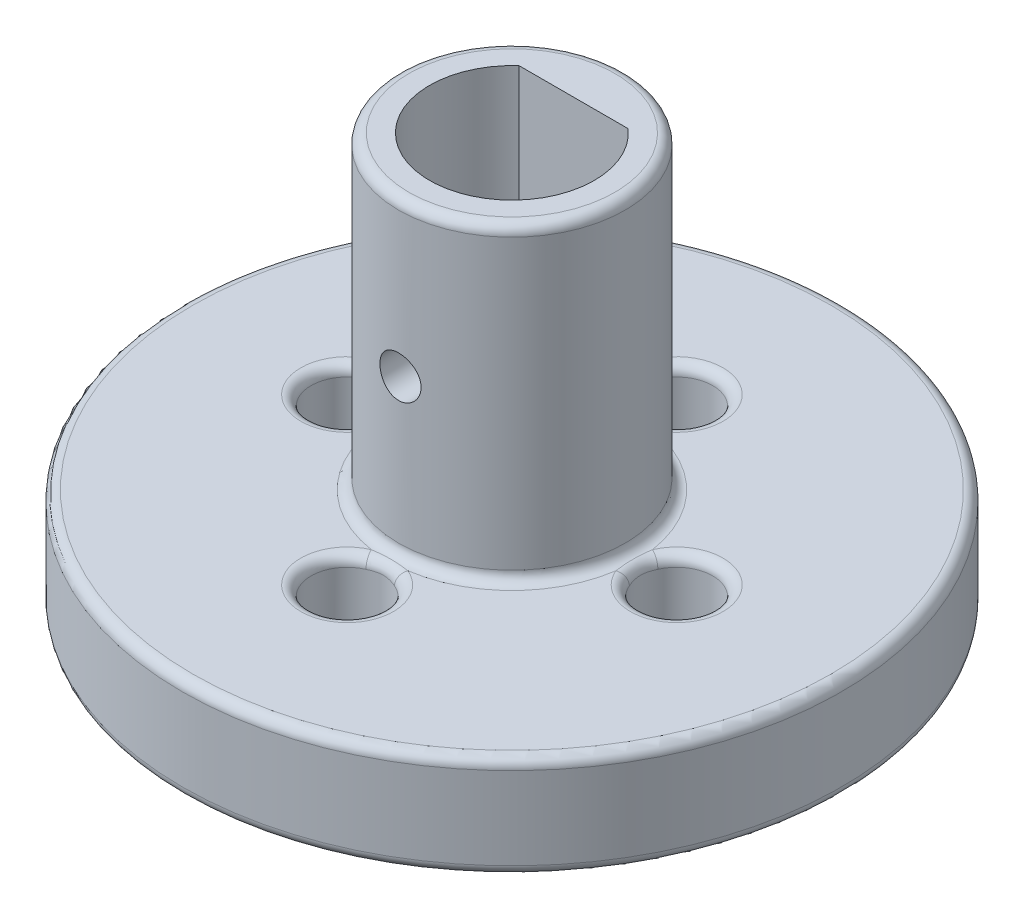
SolidWorks part; units mm, degrees
ref_plane "Front Plane" through (0, 0, 0) normal (0, 0, 1) x (1, 0, 0)
ref_plane "Top Plane" through (0, 0, 0) normal (0, 1, 0) x (1, 0, 0)
ref_plane "Right Plane" through (0, 0, 0) normal (1, 0, 0) x (0, 0, -1)
sketch "Sketch1" plane through (0, 0, 0) normal (0, 1, 0) x (1, 0, 0)
  circle A0 centre (0, 0) radius 16
  dimension "D1" = 32
extrude "Boss-Extrude1" add sketch "Sketch1" along normal blind 5
sketch "Sketch3" plane through (0, 5, 0) normal (0, 1, 0) x (1, 0, 0)
  circle A0 centre (0, 0) radius 5.5
  circle A1 centre (0, 0) radius 4
  dimension "D1" = 11
  dimension "D2" = 8
extrude "Boss-Extrude2" add sketch "Sketch3" along normal blind 15
sketch "Sketch4" plane through (0, 20, 0) normal (0, 1, 0) x (1, 0, 0)
  line L0 (-3, 3) -> (3, 3)
  line L1 (3, 3) -> (3, 4.5)
  line L2 (3, 4.5) -> (-3, 4.5)
  line L3 (-3, 4.5) -> (-3, 3)
  line L4 (-3, 4.5) -> (3, 3) construction
  line L5 (-3, 3) -> (3, 4.5) construction
  point P2 (0, 3.75)
  dimension "D1" = 3
  dimension "D2" = 6
  dimension "D3" = 1.5
extrude "Boss-Extrude3" add sketch "Sketch4" against normal up to surface (15 mm away) up to face at (0, 5, 5.5)
sketch "Sketch5" plane through (0, 5, 0) normal (0, 1, 0) x (1, 0, 0)
  circle A0 centre (0, 8) radius 1.75
  circle A1 centre (8, 0) radius 1.75
  circle A2 centre (0, -8) radius 1.75
  circle A3 centre (-8, 0) radius 1.75
  dimension "D1" = 3.5
  dimension "D2" = 8
  dimension "D3" = 4
extrude "Cut-Extrude1" cut sketch "Sketch5" against normal through all
fillet "Fillet1" radius 0.5 4 edges at (0, 20, 5.5) (0, 5, 5.5) (0, 5, 16) (0, 0, 16)
sketch "Sketch6" plane through (0, 0, 0) normal (0, 0, 1) x (1, 0, 0)
  circle A0 centre (0, 12.5) radius 1
  dimension "D1" = 2
  dimension "D2" = 12.5
extrude "Cut-Extrude2" cut sketch "Sketch6" against normal through all both and the other way through all
fillet "Fillet2" radius 0.5 4 edges at (0, 5, 9.75) (8, 5, 1.75) (0, 5, -6.25) (-8, 5, 1.75)
sketch "Sketch7" plane through (0, 0, 0) normal (0, -1, 0) x (1, 0, 0)
  circle A0 centre (0, 0) radius 4
  dimension "D1" = 8
extrude "Boss-Extrude4" add sketch "Sketch7" along normal blind 5
fillet "Fillet3" radius 0.5 2 edges at (0, 0, 4) (0, -5, -4)
